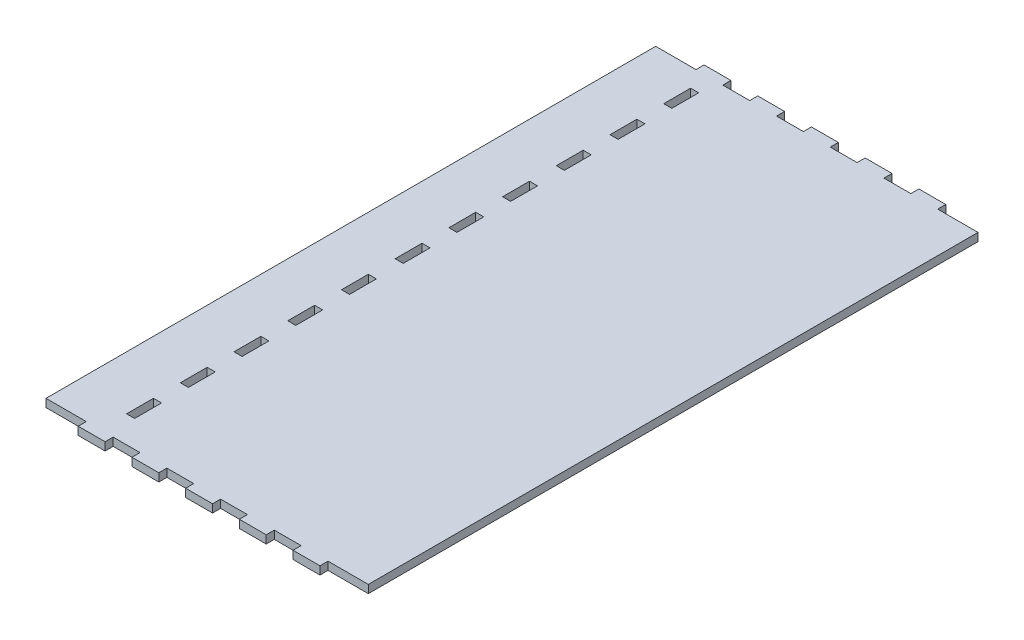
SolidWorks part; units mm, degrees
ref_plane "Front Plane" through (0, 0, 0) normal (0, 0, 1) x (1, 0, 0)
ref_plane "Top Plane" through (0, 0, 0) normal (0, 1, 0) x (1, 0, 0)
ref_plane "Right Plane" through (0, 0, 0) normal (1, 0, 0) x (0, 0, -1)
sketch "Sketch1" plane through (0, 0, 0) normal (0, 1, 0) x (1, 0, 0)
  line L1 (0, 0) -> (120, 0)
  line L2 (0, 0) -> (0, 227)
  line L3 (0, 227) -> (120, 227)
  line L4 (120, 0) -> (120, 227)
  dimension "D1" = 120
  dimension "D2" = 227
extrude "Boss-Extrude1" add sketch "Sketch1" along normal blind 3
sketch "Sketch2" plane through (0, 0, 0) normal (0, 0, 1) x (1, 0, 0)
  line L0 (0, 0) -> (120, 0) construction
  line L1 (15, 0) -> (25, 0)
  line L2 (15, 0) -> (15, 3)
  line L3 (15, 3) -> (25, 3)
  line L4 (25, 0) -> (25, 3)
  line L5 (0, 3) -> (120, 3) construction
  line L6 (0, 3) -> (0, 0) construction
  dimension "D1" = 10
  dimension "D2" = 15
extrude "Boss-Extrude2" add sketch "Sketch2" along normal blind 3
pattern_linear "LPattern1" count 5 spacing 20 along (1, 0, 0) of "Boss-Extrude2"
sketch "Sketch3" plane through (0, 0, -227) normal (0, 0, -1) x (-1, 0, 0)
  line L0 (-120, 0) -> (0, 0) construction
  line L1 (-95, 0) -> (-105, 0)
  line L2 (-95, 0) -> (-95, 3)
  line L3 (-95, 3) -> (-105, 3)
  line L4 (-105, 0) -> (-105, 3)
  line L5 (-120, 3) -> (0, 3) construction
  line L7 (-120, 3) -> (-120, 0) construction
  dimension "D1" = 15
  dimension "D2" = 10
extrude "Boss-Extrude3" add sketch "Sketch3" along normal blind 3
pattern_linear "LPattern2" count 5 spacing 20 along (-1, 0, 0) of "Boss-Extrude3"
sketch "Sketch4" plane through (0, 3, 0) normal (0, 1, 0) x (1, 0, 0)
  line L0 (0, 0) -> (15, 0) construction
  line L1 (20, 10) -> (23, 10)
  line L2 (20, 10) -> (20, 20)
  line L3 (20, 20) -> (23, 20)
  line L4 (23, 10) -> (23, 20)
  line L5 (0, 227) -> (0, 0) construction
  dimension "D1" = 10
  dimension "D2" = 10
  dimension "D3" = 3
  dimension "D4" = 20
extrude "Cut-Extrude1" cut sketch "Sketch4" against normal through all
pattern_linear "LPattern3" count 11 spacing 20 along (0, 0, -1) of "Cut-Extrude1"
